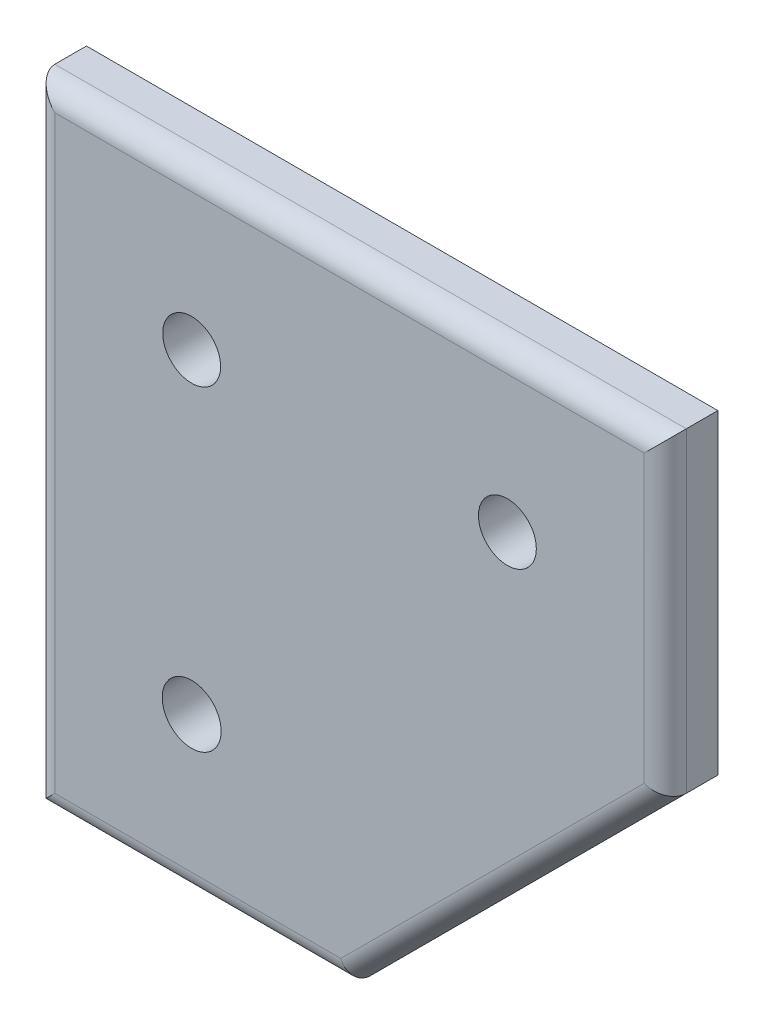
SolidWorks part; units mm, degrees
ref_plane "Front Plane" through (0, 0, 0) normal (0, 0, 1) x (1, 0, 0)
ref_plane "Top Plane" through (0, 0, 0) normal (0, 1, 0) x (1, 0, 0)
ref_plane "Right Plane" through (0, 0, 0) normal (1, 0, 0) x (0, 0, -1)
sketch "Sketch1" plane through (0, 0, 0) normal (0, 0, 1) x (1, 0, 0)
  line L0 (38.1, -38.1) -> (76.2, 0)
  line L2 (0, 0) -> (0, 38.1)
  line L3 (0, 38.1) -> (76.2, 38.1)
  line L4 (76.2, 0) -> (76.2, 38.1)
  line L6 (0, 0) -> (0, -38.1)
  line L7 (0, -38.1) -> (38.1, -38.1)
  dimension "D1" = 38.1
  dimension "D2" = 76.2
  dimension "D3" = 38.1
  dimension "D4" = 135
  dimension "D5" = 38.1
extrude "Boss-Extrude1" add sketch "Sketch1" along normal blind 6.35
sketch "Sketch2" plane through (0, 0, 6.35) normal (0, 0, 1) x (1, 0, 0)
  line L0 (0, 19.05) -> (76.1978, 19.05) construction
  line L2 (0, 38.1) -> (0, -38.1) construction
  line L3 (0, 38.1) -> (0, -38.1) construction
  line L4 (76.2, 0) -> (76.2, 38.1) construction
  line L6 (76.2, 38.1) -> (0, 38.1) construction
  line L7 (19.05, 19.05) -> (19.05, -38.1) construction
  line L10 (0, -38.1) -> (38.1, -38.1) construction
  circle A0 centre (19.05, 19.05) radius 3.4925
  circle A1 centre (57.15, 19.05) radius 3.4925
  circle A2 centre (19.05, -19.05) radius 3.556
  dimension "D1" = 6.985
  dimension "D2" = 6.985
  dimension "D3" = 19.05
  dimension "D4" = 19.05
  dimension "D7" = 7.112
  dimension "D5" = 19.05
  dimension "D6" = 19.05
  dimension "D8" = 19.05
extrude "Cut-Extrude1" cut sketch "Sketch2" against normal blind 6.35
fillet "Fillet1" radius 2.54 5 edges at (19.05, -38.1, 6.35) (76.2, 19.05, 6.35) (38.1, 38.1, 6.35) (0, 0, 6.35) (57.15, -19.05, 6.35)
